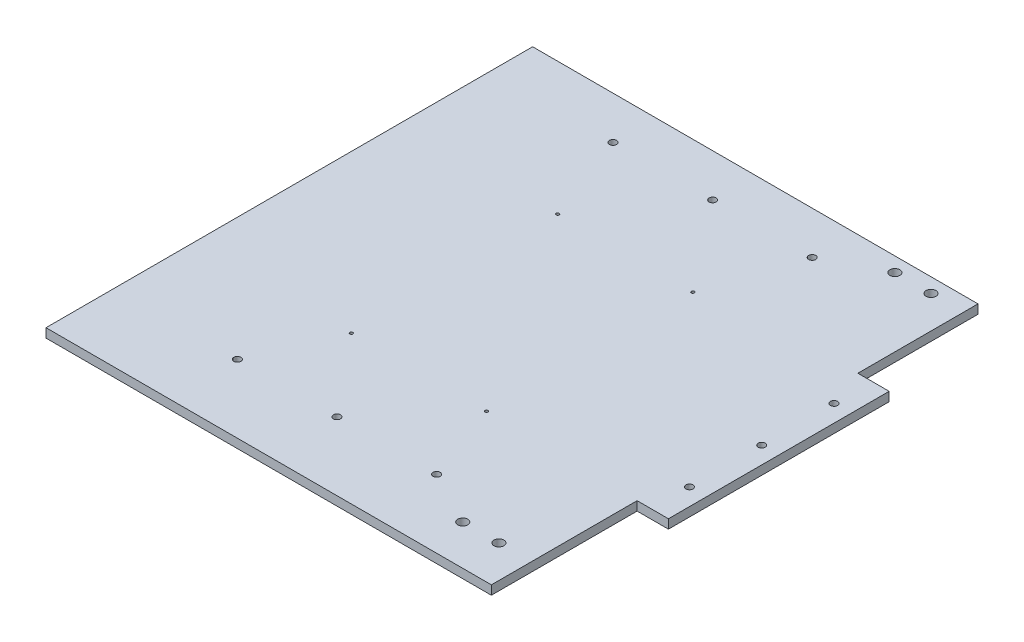
SolidWorks part; units mm, degrees
material "Cedar"
ref_plane "Front Plane" through (0, 0, 0) normal (0, 0, 1) x (1, 0, 0)
ref_plane "Top Plane" through (0, 0, 0) normal (0, 1, 0) x (1, 0, 0)
ref_plane "Right Plane" through (0, 0, 0) normal (1, 0, 0) x (0, 0, -1)
sketch "Sketch1" plane through (0, 0, 0) normal (0, 1, 0) x (1, 0, 0)
  line L0 (72.8376, -16.2766) -> (72.8376, -52.4668) construction
  line L1 (-156.5, -171) -> (156.5, -171)
  line L2 (-156.5, -171) -> (-156.5, 171)
  line L3 (-156.5, 171) -> (156.5, 171)
  line L4 (156.5, -171) -> (156.5, 171)
  line L5 (-156.5, -171) -> (156.5, 171) construction
  line L6 (-156.5, 171) -> (156.5, -171) construction
  point P0 (0, 0)
  dimension "D1" = 342
  dimension "D2" = 313
extrude "Boss-Extrude1" add sketch "Sketch1" against normal blind 6.35
ref_plane "Plane1" through (0, 0, -9) normal (0, 0, -1) x (-1, 0, 0)
sketch "Sketch3" plane through (0, 0, 0) normal (0, 1, 0) x (1, 0, 0)
  line L0 (156.5, 9) -> (-156.5, 9) construction
  line L1 (156.5, -171) -> (156.5, 171) construction
  line L2 (-156.5, 171) -> (-156.5, -171) construction
  line L3 (55, 9) -> (-55, 9) construction
  line L4 (156.5, 86.5702) -> (156.5, -68.5702)
  line L5 (156.5, -68.5702) -> (178.5, -68.5702)
  line L6 (178.5, -68.5702) -> (178.5, 86.5702)
  line L7 (178.5, 86.5702) -> (156.5, 86.5702)
  line L8 (166.5, 59.8) -> (166.5, 9) construction
  circle A0 centre (166.5, 9) radius 2.5
  circle A1 centre (166.5, -41.8) radius 2.5
  circle A2 centre (166.5, 59.8) radius 2.5
  point P10 (156.5, 9)
  dimension "D2" = 5
  dimension "D4" = 5
  dimension "D5" = 50.8
  dimension "D1" = 22
  dimension "D3" = 10
  dimension "D6" = 0
extrude "Boss-Extrude2" add sketch "Sketch3" against normal blind 6.35
sketch "Sketch2" plane through (0, 0, 0) normal (0, 1, 0) x (1, 0, 0)
  line L0 (156.5, 9) -> (-156.5, 9) construction
  line L1 (156.5, -171) -> (156.5, -68.5702) construction
  line L2 (-156.5, 171) -> (-156.5, -171) construction
  line L3 (0, -123) -> (0, -171) construction
  line L4 (55, 9) -> (-55, 9) construction
  line L5 (156.5, -123) -> (-156.5, -123) construction
  line L6 (-156.5, -171) -> (156.5, -171) construction
  circle A0 centre (0, -123) radius 2.5
  circle A1 centre (-70, -123) radius 2.5
  circle A2 centre (70, -123) radius 2.5
  circle A3 centre (-70, 141) radius 2.5
  circle A4 centre (0, 141) radius 2.5
  circle A5 centre (70, 141) radius 2.5
  dimension "D2" = 5
  dimension "D3" = 5
  dimension "D4" = 70
  dimension "D1" = 132
extrude "Cut-Extrude1" cut sketch "Sketch2" against normal through all
sketch "Sketch4" plane through (0, 0, 0) normal (0, 1, 0) x (1, 0, 0)
  line L0 (156.5, -171) -> (156.5, -68.5702) construction
  line L1 (108.24, -142.84) -> (133.64, -142.84) construction
  line L2 (-156.5, -171) -> (156.5, -171) construction
  circle A0 centre (133.64, -142.84) radius 3.5
  circle A1 centre (108.24, -142.84) radius 3.5
  dimension "D1" = 7
  dimension "D2" = 7
  dimension "D3" = 25.4
  dimension "D4" = 22.86
  dimension "D5" = 28.16
extrude "Cut-Extrude2" cut sketch "Sketch4" against normal through all
mirror "Mirror1" about plane through (0, 0, -9) normal (0, 0, -1) of "Cut-Extrude2"
sketch "Sketch5" plane through (0, 0, 0) normal (0, 1, 0) x (1, 0, 0)
  circle A33 centre (49.1492, 77.944) radius 1.05
  circle A34 centre (49.1492, -67.056) radius 1.05
  circle A35 centre (-45.8508, 77.944) radius 1.05
  circle A36 centre (-45.8508, -67.056) radius 1.05
extrude "Cut-Extrude3" cut sketch "Sketch5" against normal through all
